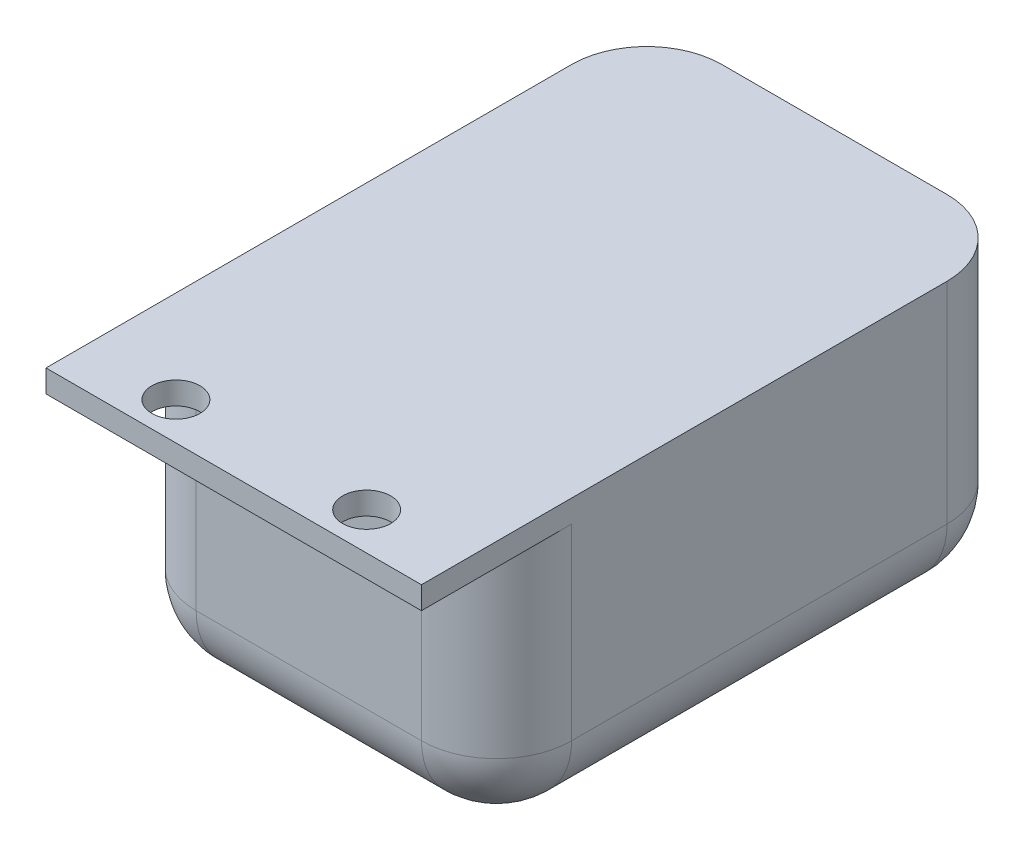
SolidWorks part; units mm, degrees
material "ABS"
ref_plane "Front Plane" through (0, 0, 0) normal (0, 0, 1) x (1, 0, 0)
ref_plane "Top Plane" through (0, 0, 0) normal (0, 1, 0) x (1, 0, 0)
ref_plane "Right Plane" through (0, 0, 0) normal (1, 0, 0) x (0, 0, -1)
sketch "Sketch1" plane through (0, 0, 0) normal (1, 0, 0) x (0, 0, -1)
  line L1 (-35, 17.5) -> (35, 17.5)
  line L2 (-35, 17.5) -> (-35, -17.5)
  line L3 (-35, -17.5) -> (35, -17.5)
  line L4 (35, 17.5) -> (35, -17.5)
  line L5 (-35, 17.5) -> (35, -17.5) construction
  line L6 (-35, -17.5) -> (35, 17.5) construction
  point P0 (0, 0)
  dimension "D1" = 70
  dimension "D2" = 35
extrude "Boss-Extrude1" add sketch "Sketch1" along normal blind 50
shell "Shell1" thickness 3
sketch "Sketch2" plane through (0, 17.5, 0) normal (0, 1, 0) x (1, 0, 0)
  line L0 (0, -35) -> (0, 35)
  line L1 (0, 35) -> (50, 35)
  line L2 (50, 35) -> (50, -35)
  line L3 (50, -35) -> (0, -35)
extrude "Boss-Extrude2" add sketch "Sketch2" along normal blind 3
sketch "Sketch4" plane through (0, -17.5, 0) normal (0, -1, 0) x (1, 0, 0)
  circle A0 centre (25, 0) radius 6.5
  dimension "D1" = 13
extrude "Boss-Extrude3" add sketch "Sketch4" along normal blind 6
sketch "Sketch5" plane through (0, -23.5, 0) normal (0, -1, 0) x (1, 0, 0)
  circle A0 centre (25, 0) radius 4.5
  circle A1 centre (25, 0) radius 6.5 construction
  dimension "D1" = 2
extrude "Cut-Extrude1" cut sketch "Sketch5" against normal up to next
sketch "Sketch6" plane through (0, 0, 35) normal (0, 0, 1) x (1, 0, 0)
  line L0 (0, 20.5) -> (50, 20.5)
  line L1 (50, 20.5) -> (50, 17.5)
  line L2 (50, 20.5) -> (50, -17.5) construction
  line L3 (50, 17.5) -> (0, 17.5)
  line L4 (0, 20.5) -> (0, -17.5) construction
  line L5 (0, 17.5) -> (0, 20.5)
  dimension "D1" = 3
extrude "Boss-Extrude4" add sketch "Sketch6" along normal blind 10
sketch "Sketch7" plane through (0, -17.5, 0) normal (0, -1, 0) x (-1, 0, 0)
  line L0 (-25, 0) -> (-25, -45) construction
  line L1 (0, -45) -> (-50, -45) construction
  line L2 (0, -45) -> (0, -35) construction
  line L3 (0, -40) -> (-50, -40) construction
  line L4 (-50, -45) -> (-50, -35) construction
sketch "Sketch8" plane through (0, 17.5, 0) normal (0, -1, 0) x (1, 0, 0)
  line L0 (0, 40) -> (50, 40) construction
  line L1 (25, 0) -> (25, 45) construction
  circle A0 centre (12.3, 40) radius 3.2
  dimension "D1" = 6.4
  dimension "D2" = 12.7
extrude "Cut-Extrude3" cut sketch "Sketch8" against normal through all
sketch "Sketch9" plane through (0, 17.5, 0) normal (0, -1, 0) x (1, 0, 0)
  line L0 (0, 40) -> (50, 40) construction
  line L1 (25, 0) -> (25, 45) construction
  circle A0 centre (37.7, 40) radius 3.2
  dimension "D1" = 6.4
  dimension "D2" = 12.7
extrude "Cut-Extrude4" cut sketch "Sketch9" against normal through all
fillet "Fillet1" radius 10 8 edges at (0, 1.5, -35) (50, 1.5, -35) (0, -17.5, 0) (50, -17.5, 0) (25, -17.5, -35) (25, -17.5, 35) (0, 0, 35) (50, 0, 35)
fillet "Fillet2" radius 10 8 edges at (3, 1.5, -32) (47, 1.5, -32) (3, 1.5, 32) (47, 1.5, 32) (3, -14.5, 0) (25, -14.5, 32) (25, -14.5, -32) (47, -14.5, 0)
